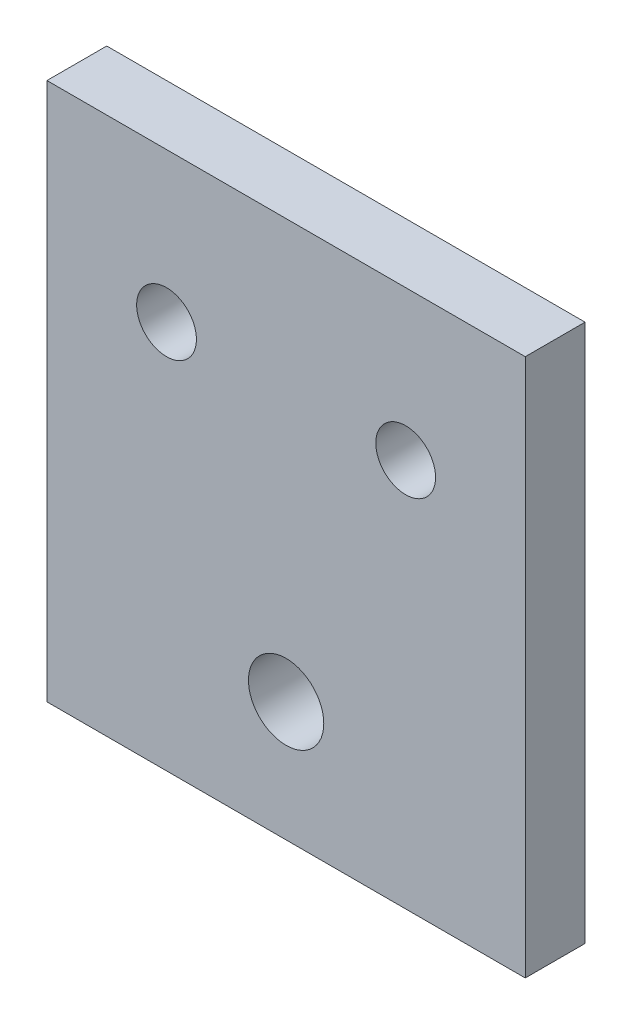
SolidWorks part; units mm, degrees
material "1060 Alloy"
ref_plane "Front Plane" through (0, 0, 0) normal (0, 0, 1) x (1, 0, 0)
ref_plane "Top Plane" through (0, 0, 0) normal (0, 1, 0) x (1, 0, 0)
ref_plane "Right Plane" through (0, 0, 0) normal (1, 0, 0) x (0, 0, -1)
sketch "Sketch1" plane through (0, 0, 0) normal (0, 0, 1) x (1, 0, 0)
  line L1 (-25.4, -28.575) -> (25.4, -28.575)
  line L2 (-25.4, -28.575) -> (-25.4, 28.575)
  line L3 (-25.4, 28.575) -> (25.4, 28.575)
  line L4 (25.4, -28.575) -> (25.4, 28.575)
  line L5 (-25.4, -28.575) -> (25.4, 28.575) construction
  line L6 (-25.4, 28.575) -> (25.4, -28.575) construction
  point P0 (0, 0)
  dimension "D1" = 57.15
  dimension "D2" = 50.8
extrude "Boss-Extrude1" add sketch "Sketch1" along normal blind 6.35
sketch "Sketch4" plane through (0, 0, 6.35) normal (0, 0, 1) x (1, 0, 0)
  line L0 (0, 28.575) -> (0, -28.575) construction
  line L1 (25.4, 28.575) -> (-25.4, 28.575) construction
  line L2 (-25.4, -28.575) -> (25.4, -28.575) construction
  line L3 (-12.7, 12.7) -> (12.7, 12.7) construction
  line L4 (-25.4, 28.575) -> (-25.4, -28.575) construction
  circle A0 centre (0, -15.875) radius 4
  circle A1 centre (-12.7, 12.7) radius 3.175
  circle A2 centre (12.7, 12.7) radius 3.175
  point P12 (0, 12.7)
  dimension "D1" = 8
  dimension "D2" = 6.35
  dimension "D3" = 6.35
  dimension "D4" = 25.4
  dimension "D5" = 12.7
  dimension "D6" = 28.575
extrude "Cut-Extrude1" cut sketch "Sketch4" against normal up to surface (6.35 mm away) up to face at (0, 0, 0)
